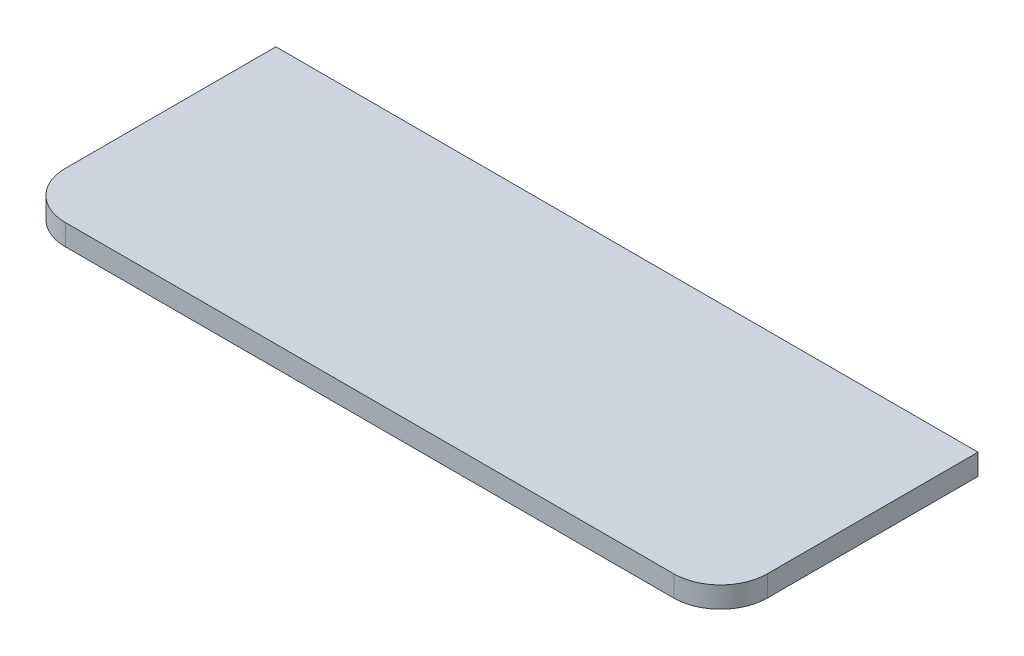
SolidWorks part; units mm, degrees
ref_plane "Спереди" through (0, 0, 0) normal (0, 0, 1) x (1, 0, 0)
ref_plane "Сверху" through (0, 0, 0) normal (0, 1, 0) x (1, 0, 0)
ref_plane "Справа" through (0, 0, 0) normal (1, 0, 0) x (0, 0, -1)
sketch "Эскиз1" plane through (0, 0, 0) normal (0, 1, 0) x (1, 0, 0)
  line L1 (-32.6549, 18.1514) -> (567.3451, 18.1514)
  line L2 (-32.6549, 18.1514) -> (-32.6549, -161.8486)
  line L3 (7.3451, -201.8486) -> (527.3451, -201.8486)
  line L4 (567.3451, 18.1514) -> (567.3451, -161.8486)
  arc A0 (527.3451, -201.8486) -> (567.3451, -161.8486) centre (527.3451, -161.8486) ccw
  arc A1 (-32.6549, -161.8486) -> (7.3451, -201.8486) centre (7.3451, -161.8486) ccw
  point P8 (-32.6549, -201.8486)
  dimension "D3" = 40
  dimension "D1" = 600
  dimension "D2" = 220
extrude "Бобышка-Вытянуть1" add sketch "Эскиз1" along normal blind 18
